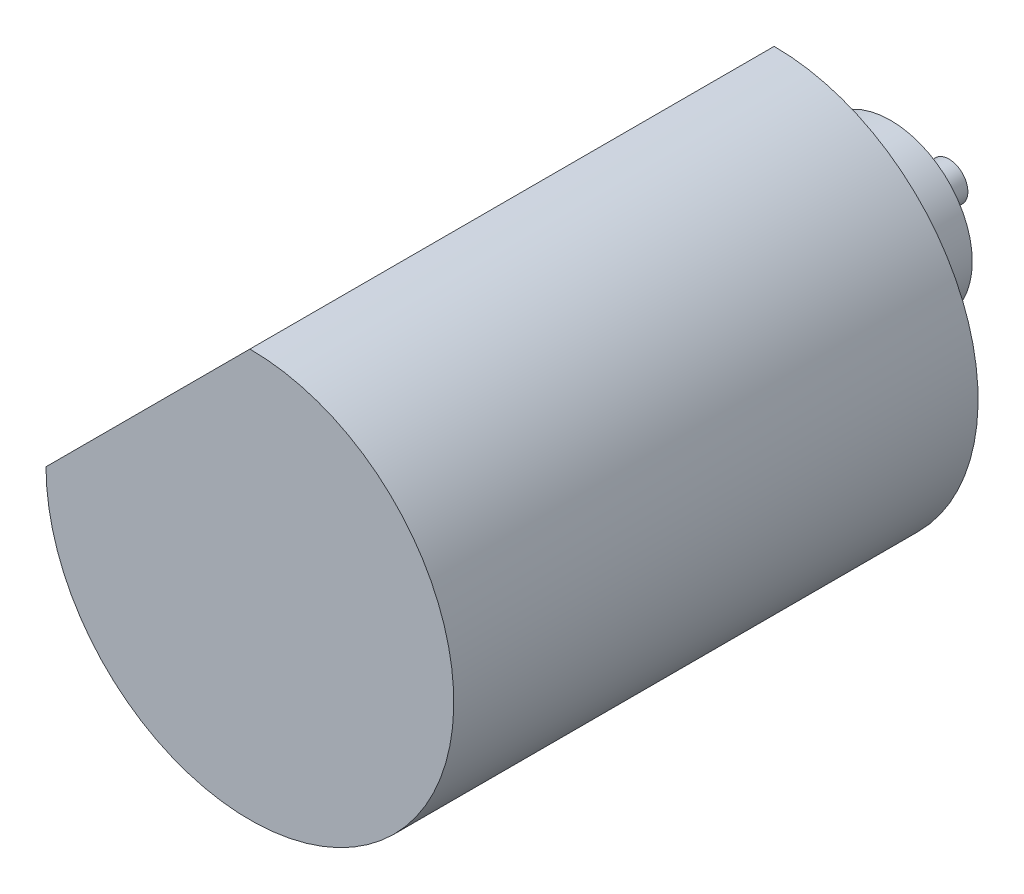
SolidWorks part; units mm, degrees
ref_plane "前视基准面" through (0, 0, 0) normal (0, 0, 1) x (1, 0, 0)
ref_plane "上视基准面" through (0, 0, 0) normal (0, 1, 0) x (1, 0, 0)
ref_plane "右视基准面" through (0, 0, 0) normal (1, 0, 0) x (0, 0, -1)
sketch "草图1" plane through (0, 0, 0) normal (0, 0, 1) x (1, 0, 0)
  line L0 (0, 0) -> (0, 17.5) construction
  line L1 (0, 0) -> (-17.5, 0) construction
  line L2 (0, 17.5) -> (-17.5, 0)
  arc A0 (-17.5, 0) -> (0, 17.5) centre (0, 0) ccw
  dimension "D1" = 35
  dimension "D2" = 90
extrude "凸台-拉伸1" add sketch "草图1" along normal blind 45
sketch "草图2" plane through (0, 0, 0) normal (0, 0, -1) x (-1, 0, 0)
  circle A0 centre (0, 0) radius 1.625
  dimension "D1" = 3.25
extrude "凸台-拉伸2" add sketch "草图2" along normal blind 15
sketch "草图3" plane through (0, 0, 0) normal (0, 0, -1) x (-1, 0, 0)
  circle A0 centre (0, 0) radius 7
  dimension "D1" = 14
extrude "凸台-拉伸3" add sketch "草图3" along normal blind 10
